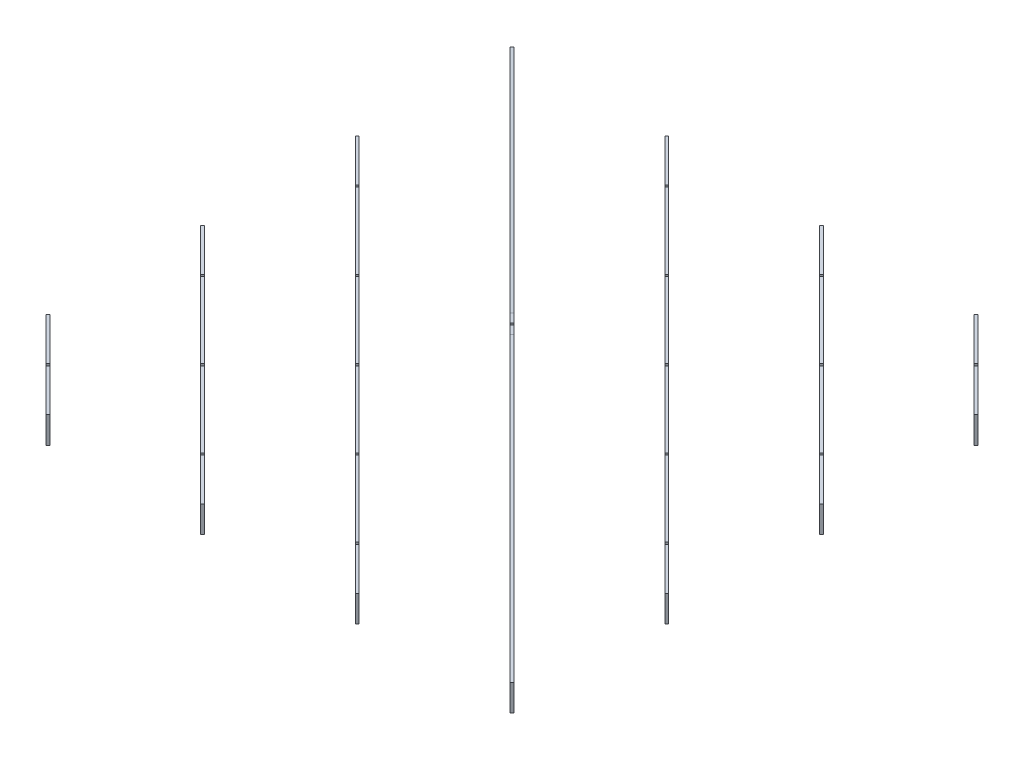
SolidWorks part; units mm, degrees
material "1.0553 (S355J0)"
ref_plane "Front" through (0, 0, 0) normal (0, 0, 1) x (1, 0, 0)
ref_plane "Top" through (0, 0, 0) normal (0, 1, 0) x (1, 0, 0)
ref_plane "Right" through (0, 0, 0) normal (1, 0, 0) x (0, 0, -1)
sketch "Sketch1" plane through (0, 0, 0) normal (0, 1, 0) x (1, 0, 0)
  line L0 (-525, -525) -> (-525, 525) construction
  line L1 (-625, 625) -> (625, 625) construction
  line L2 (-625, 625) -> (-625, -625) construction
  line L3 (-625, -625) -> (625, -625) construction
  line L4 (625, 625) -> (625, -625) construction
  line L5 (-625, 625) -> (625, -625) construction
  line L6 (-625, -625) -> (625, 625) construction
  line L7 (-525, 525) -> (525, 525) construction
  line L8 (-525, 350) -> (525, 350) construction
  line L9 (-525, 175) -> (525, 175) construction
  line L10 (-525, 0) -> (525, 0) construction
  line L11 (-525, -175) -> (525, -175) construction
  line L12 (-525, -350) -> (525, -350) construction
  line L13 (-525, -525) -> (525, -525) construction
  line L14 (-350, -525) -> (-350, 525) construction
  line L15 (-175, -525) -> (-175, 525) construction
  line L16 (0, -525) -> (0, 525) construction
  line L17 (175, -525) -> (175, 525) construction
  line L18 (350, -525) -> (350, 525) construction
  line L19 (525, -525) -> (525, 525) construction
  line L20 (-620, 625) -> (620, 625) construction
  line L23 (625, 620) -> (625, -620) construction
  point P0 (0, 0)
  dimension "D5" = 175
  dimension "D3" = 7
  dimension "D4" = 7
sketch "Sketch2" plane through (0, 0, 0) normal (0, 1, 0) x (1, 0, 0)
  line L0 (-625, 625) -> (625, -625) construction
  line L1 (622.8787, -622.8787) -> (-622.8787, -622.8787) construction
  line L2 (622.8787, -622.8787) -> (622.8787, 622.8787) construction
  line L3 (622.8787, 622.8787) -> (-622.8787, 622.8787) construction
  line L4 (-622.8787, -622.8787) -> (-622.8787, 622.8787) construction
  line L5 (622.8787, -622.8787) -> (-622.8787, 622.8787) construction
  line L6 (622.8787, 622.8787) -> (-622.8787, -622.8787) construction
  line L7 (-272.8787, 622.8787) -> (622.8787, -272.8787) construction
  line L8 (77.1213, 622.8787) -> (622.8787, 77.1213) construction
  line L9 (427.1213, 622.8787) -> (622.8787, 427.1213) construction
  line L10 (-622.8787, 272.8787) -> (272.8787, -622.8787) construction
  line L11 (-622.8787, -77.1213) -> (-77.1213, -622.8787) construction
  line L12 (-622.8787, -427.1213) -> (-427.1213, -622.8787) construction
  line L13 (-625, -429.2426) -> (-429.2426, -625)
  line L14 (-625, -79.2426) -> (-79.2426, -625)
  line L15 (-625, 270.7574) -> (270.7574, -625)
  line L16 (625, -620.7574) -> (-620.7574, 625)
  line L17 (-275, 620.7574) -> (620.7574, -275)
  line L18 (75, 620.7574) -> (620.7574, 75)
  line L19 (425, 620.7574) -> (620.7574, 425)
  line L20 (-620.7574, -425) -> (-425, -620.7574)
  line L21 (-620.7574, -75) -> (-75, -620.7574)
  line L22 (-620.7574, 275) -> (275, -620.7574)
  line L23 (620.7574, -625) -> (-625, 620.7574)
  line L24 (-270.7574, 625) -> (625, -270.7574)
  line L25 (79.2426, 625) -> (625, 79.2426)
  line L26 (429.2426, 625) -> (625, 429.2426)
  line L27 (-625, 625) -> (625, 625) construction
  line L29 (-625, -429.2426) -> (-620.7574, -425)
  line L30 (-429.2426, -625) -> (-425, -620.7574)
  line L31 (-625, -79.2426) -> (-620.7574, -75)
  line L32 (-79.2426, -625) -> (-75, -620.7574)
  line L33 (-625, 270.7574) -> (-620.7574, 275)
  line L34 (270.7574, -625) -> (275, -620.7574)
  line L35 (625, -620.7574) -> (620.7574, -625)
  line L36 (-620.7574, 625) -> (-625, 620.7574)
  line L37 (-275, 620.7574) -> (-270.7574, 625)
  line L38 (620.7574, -275) -> (625, -270.7574)
  line L39 (75, 620.7574) -> (79.2426, 625)
  line L40 (620.7574, 75) -> (625, 79.2426)
  line L41 (425, 620.7574) -> (429.2426, 625)
  line L42 (620.7574, 425) -> (625, 429.2426)
  point P0 (0, 0)
extrude "Boss-Extrude1" add sketch "Sketch2" along normal blind 60
sketch "Sketch4" plane through (-2.1213, 0, 2.1213) normal (-0.7071, 0, 0.7071) x (0.7071, 0, 0.7071)
  line L0 (0, 60) -> (0, 140) construction
  line L1 (-138.4214, 60) -> (138.4214, 60) construction
  line L2 (-30, 140) -> (-880.8835, 60)
  line L3 (-880.8835, 60) -> (-30, 60)
  line L4 (-30, 60) -> (-30, 140) construction
  line L5 (30, 140) -> (-30, 140)
  line L6 (880.8835, 60) -> (30, 60)
  line L7 (30, 140) -> (880.8835, 60)
  line L8 (-30, 60) -> (30, 60)
  dimension "D1" = 80
  dimension "D2" = 30
extrude "Boss-Extrude2" add sketch "Sketch4" against normal up to vertex
sketch "Sketch5" plane through (-527.1213, 0, 527.1213) normal (-0.7071, 0, 0.7071) x (0.7071, 0, 0.7071)
  line L0 (0, 0) -> (0, 60) construction
  line L1 (-138.4214, 60) -> (138.4214, 60) construction
  line L2 (-247.4874, 0) -> (-247.4874, 60) construction
  line L3 (494.9747, 0) -> (-247.4874, 0) construction
  line L4 (-742.4621, 0) -> (0, 0) construction
  line L5 (-385.9087, 60) -> (385.9087, 60) construction
  line L6 (-494.9747, 0) -> (-494.9747, 60) construction
  line L7 (247.4874, 0) -> (-494.9747, 0) construction
  line L8 (123.7437, 0) -> (-618.7184, 0) construction
  line L9 (-633.3961, 60) -> (633.3961, 60) construction
  line L10 (497.9747, 30) -> (491.9747, 90) construction
  line L11 (-250.4874, 90) -> (-244.4874, 90)
  line L12 (-250.4874, 90) -> (-250.4874, 30)
  line L13 (-250.4874, 30) -> (-244.4874, 30)
  line L14 (-244.4874, 90) -> (-244.4874, 30)
  line L15 (-250.4874, 90) -> (-244.4874, 30) construction
  line L16 (-250.4874, 30) -> (-244.4874, 90) construction
  line L17 (-497.9747, 90) -> (-491.9747, 90)
  line L18 (-497.9747, 90) -> (-497.9747, 30)
  line L19 (-497.9747, 30) -> (-491.9747, 30)
  line L20 (-491.9747, 90) -> (-491.9747, 30)
  line L21 (-497.9747, 90) -> (-491.9747, 30) construction
  line L22 (-497.9747, 30) -> (-491.9747, 90) construction
  line L23 (-3, 90) -> (3, 90)
  line L24 (-3, 90) -> (-3, 30)
  line L25 (-3, 30) -> (3, 30)
  line L26 (3, 90) -> (3, 30)
  line L27 (-3, 90) -> (3, 30) construction
  line L28 (-3, 30) -> (3, 90) construction
  line L29 (497.9747, 90) -> (491.9747, 30) construction
  line L30 (250.4874, 30) -> (244.4874, 90) construction
  line L31 (250.4874, 90) -> (244.4874, 30) construction
  line L32 (494.9747, 0) -> (494.9747, 60) construction
  line L33 (247.4874, 0) -> (247.4874, 60) construction
  line L34 (491.9747, 90) -> (491.9747, 30)
  line L35 (497.9747, 30) -> (491.9747, 30)
  line L36 (497.9747, 90) -> (497.9747, 30)
  line L37 (497.9747, 90) -> (491.9747, 90)
  line L38 (244.4874, 90) -> (244.4874, 30)
  line L39 (250.4874, 30) -> (244.4874, 30)
  line L40 (250.4874, 90) -> (250.4874, 30)
  line L41 (250.4874, 90) -> (244.4874, 90)
  circle A0 centre (-497.9747, 30) radius 1.5
  circle A1 centre (-491.9747, 30) radius 1.5
  circle A2 centre (-250.4874, 30) radius 1.5
  circle A3 centre (-244.4874, 30) radius 1.5
  circle A4 centre (-3, 30) radius 1.5
  circle A5 centre (3, 30) radius 1.5
  circle A6 centre (244.4874, 30) radius 1.5
  circle A7 centre (250.4874, 30) radius 1.5
  circle A8 centre (491.9747, 30) radius 1.5
  circle A9 centre (497.9747, 30) radius 1.5
  line M11 (138.4214, 60) -> (-138.4214, 60)
  dimension "D7" = 3
  dimension "D8" = 3
  dimension "D9" = 3
  dimension "D10" = 3
  dimension "D11" = 3
  dimension "D12" = 3
  dimension "D1" = 3
  dimension "D2" = 3
  dimension "D3" = 3
  dimension "D4" = 60
  dimension "D5" = 60
  dimension "D6" = 60
extrude "Cut-Extrude1" cut sketch "Sketch5" against normal up to surface (500.9747 mm away) contours L35 A9 L36 L37 L34 A8 | A8 L34 L35 | A8 L35 L34 | A9 L36 L35 | A9 L35 L36 | L39 A7 L40 L41 L38 A6 | A6 L38 L39 | A6 L39 L38 | A7 L39 L40 | A7 L40 L39 | A5 L26 L24 A4 L25 M11 | L25 A4 L24 | L24 A4 L25 | L26 A5 L25 | L25 A5 L26 | A3 L14 L11 L12 A2 L13 | L13 A2 L12 | L12 A2 L13 | L14 A3 L13 | L13 A3 L14 | A1 L20 L17 L18 A0 L19 | L19 A0 L18 | L18 A0 L19 | L20 A1 L19 | L19 A1 L20 up to face at (-172.8787, 30, 172.8787)
sketch "Sketch6" plane through (527.1213, 0, -527.1213) normal (0.7071, 0, -0.7071) x (-0.7071, 0, -0.7071)
  line L4 (-138.4214, 0) -> (138.4214, 0)
  line L5 (138.4214, 0) -> (138.4214, 60)
  line L6 (138.4214, 60) -> (-138.4214, 60)
  line L7 (-138.4214, 60) -> (-138.4214, 0)
  line L8 (-138.4214, 0) -> (138.4214, 0)
  line L9 (138.4214, 0) -> (138.4214, 60)
  line L10 (138.4214, 60) -> (-138.4214, 60)
  line L11 (-138.4214, 60) -> (-138.4214, 0)
  line L12 (497.9747, 90) -> (491.9747, 90)
  line L13 (491.9747, 90) -> (491.9747, 30)
  line L14 (491.9747, 30) -> (497.9747, 30)
  line L15 (497.9747, 30) -> (497.9747, 90)
  line L16 (497.9747, 90) -> (491.9747, 90)
  line L17 (491.9747, 90) -> (491.9747, 30)
  line L18 (491.9747, 30) -> (497.9747, 30)
  line L19 (497.9747, 30) -> (497.9747, 90)
  line L20 (250.4874, 90) -> (244.4874, 90)
  line L21 (244.4874, 90) -> (244.4874, 30)
  line L22 (244.4874, 30) -> (250.4874, 30)
  line L23 (250.4874, 30) -> (250.4874, 90)
  line L24 (250.4874, 90) -> (244.4874, 90)
  line L25 (244.4874, 90) -> (244.4874, 30)
  line L26 (244.4874, 30) -> (250.4874, 30)
  line L27 (250.4874, 30) -> (250.4874, 90)
  line L28 (-244.4874, 30) -> (-244.4874, 90)
  line L29 (-250.4874, 30) -> (-244.4874, 30)
  line L30 (-250.4874, 90) -> (-250.4874, 30)
  line L31 (-244.4874, 90) -> (-250.4874, 90)
  line L32 (-244.4874, 30) -> (-244.4874, 90)
  line L33 (-250.4874, 30) -> (-244.4874, 30)
  line L34 (-250.4874, 90) -> (-250.4874, 30)
  line L35 (-244.4874, 90) -> (-250.4874, 90)
  line L36 (-491.9747, 30) -> (-491.9747, 90)
  line L37 (-497.9747, 30) -> (-491.9747, 30)
  line L38 (-497.9747, 90) -> (-497.9747, 30)
  line L39 (-491.9747, 90) -> (-497.9747, 90)
  line L40 (-491.9747, 30) -> (-491.9747, 90)
  line L41 (-497.9747, 30) -> (-491.9747, 30)
  line L42 (-497.9747, 90) -> (-497.9747, 30)
  line L43 (-491.9747, 90) -> (-497.9747, 90)
  line L44 (3, 90) -> (-3, 90)
  line L45 (3, 30) -> (3, 90)
  line L46 (-3, 30) -> (3, 30)
  line L47 (-3, 90) -> (-3, 30)
  line L48 (3, 90) -> (-3, 90)
  line L49 (3, 30) -> (3, 90)
  line L50 (-3, 30) -> (3, 30)
  line L51 (-3, 90) -> (-3, 30)
  circle A1 centre (-3, 30) radius 1.5
  circle A2 centre (-3, 30) radius 1.5
  circle A3 centre (3, 30) radius 1.5
  circle A4 centre (3, 30) radius 1.5
  circle A5 centre (244.4874, 30) radius 1.5
  circle A6 centre (244.4874, 30) radius 1.5
  circle A7 centre (250.4874, 30) radius 1.5
  circle A8 centre (250.4874, 30) radius 1.5
  circle A9 centre (491.9747, 30) radius 1.5
  circle A10 centre (491.9747, 30) radius 1.5
  circle A11 centre (497.9747, 30) radius 1.5
  circle A12 centre (497.9747, 30) radius 1.5
  circle A13 centre (-497.9747, 30) radius 1.5
  circle A14 centre (-497.9747, 30) radius 1.5
  circle A15 centre (-491.9747, 30) radius 1.5
  circle A16 centre (-491.9747, 30) radius 1.5
  circle A17 centre (-250.4874, 30) radius 1.5
  circle A18 centre (-250.4874, 30) radius 1.5
  circle A19 centre (-244.4874, 30) radius 1.5
  circle A20 centre (-244.4874, 30) radius 1.5
  dimension "D1" = 0
  dimension "D2" = 0
  dimension "D3" = 0
  dimension "D4" = 0
  dimension "D5" = 0
  dimension "D6" = 0
  dimension "D7" = 0
  dimension "D8" = 0
  dimension "D9" = 0
  dimension "D10" = 0
  dimension "D11" = 0
  dimension "D12" = 0
  dimension "D13" = 0
  dimension "D14" = 0
  dimension "D15" = 0
  dimension "D16" = 0
extrude "Cut-Extrude2" cut sketch "Sketch6" against normal up to surface (500.9747 mm away) contours A16 L40 L43 L42 A14 L41 | L41 A14 L42 | L42 A14 L41 | L40 A16 L41 | L41 A16 L40 | A20 L32 L35 L34 A18 L33 | L33 A18 L34 | L34 A18 L33 | L32 A20 L33 | L33 A20 L32 | A4 L49 L10 L51 A2 L50 | L49 A4 L50 | L50 A4 L49 | L50 A2 L51 | L51 A2 L50 | L25 A6 L26 | L26 A6 L25 | A8 L27 L24 L25 A6 L26 | L27 A8 L26 | L26 A8 L27 | L17 A10 L18 | L18 A10 L17 | A12 L19 L16 L17 A10 L18 | L19 A12 L18 | L18 A12 L19 up to face at (172.8787, 30, -172.8787)
sketch "Sketch7" plane through (-2.1213, 0, 2.1213) normal (-0.7071, 0, 0.7071) x (0.7071, 0, 0.7071)
  line L0 (0, 140) -> (0, 0) construction
  line L1 (30, 140) -> (-30, 140) construction
  line L2 (123.7437, 0) -> (-618.7184, 0) construction
  line L3 (-3, 210) -> (3, 210)
  line L4 (-3, 210) -> (-3, 70)
  line L5 (-3, 70) -> (3, 70)
  line L6 (3, 210) -> (3, 70)
  line L7 (-3, 210) -> (3, 70) construction
  line L8 (-3, 70) -> (3, 210) construction
  line L9 (-250.4874, 30) -> (-244.4874, 30)
  line L10 (-250.4874, 30) -> (-250.4874, -30)
  line L11 (-250.4874, -30) -> (-244.4874, -30)
  line L12 (-244.4874, 30) -> (-244.4874, -30)
  line L13 (-250.4874, 30) -> (-244.4874, -30) construction
  line L14 (-250.4874, -30) -> (-244.4874, 30) construction
  line L15 (247.4874, 0) -> (-494.9747, 0) construction
  line L16 (-497.9747, 30) -> (-491.9747, 30)
  line L17 (-497.9747, 30) -> (-497.9747, -30)
  line L18 (-497.9747, -30) -> (-491.9747, -30)
  line L19 (-491.9747, 30) -> (-491.9747, -30)
  line L20 (-497.9747, 30) -> (-491.9747, -30) construction
  line L21 (-497.9747, -30) -> (-491.9747, 30) construction
  line L22 (-883.8835, 0) -> (883.8835, 0) construction
  line L23 (-742.4621, 0) -> (0, 0) construction
  line L24 (-745.4621, 30) -> (-739.4621, 30)
  line L25 (-745.4621, 30) -> (-745.4621, -30)
  line L26 (-745.4621, -30) -> (-739.4621, -30)
  line L27 (-739.4621, 30) -> (-739.4621, -30)
  line L28 (-745.4621, 30) -> (-739.4621, -30) construction
  line L29 (-745.4621, -30) -> (-739.4621, 30) construction
  line L30 (745.4621, -30) -> (739.4621, 30) construction
  line L31 (745.4621, 30) -> (739.4621, -30) construction
  line L32 (497.9747, -30) -> (491.9747, 30) construction
  line L33 (497.9747, 30) -> (491.9747, -30) construction
  line L34 (250.4874, -30) -> (244.4874, 30) construction
  line L35 (250.4874, 30) -> (244.4874, -30) construction
  line L36 (739.4621, 30) -> (739.4621, -30)
  line L37 (745.4621, -30) -> (739.4621, -30)
  line L38 (745.4621, 30) -> (745.4621, -30)
  line L39 (745.4621, 30) -> (739.4621, 30)
  line L40 (491.9747, 30) -> (491.9747, -30)
  line L41 (497.9747, -30) -> (491.9747, -30)
  line L42 (497.9747, 30) -> (497.9747, -30)
  line L43 (497.9747, 30) -> (491.9747, 30)
  line L44 (244.4874, 30) -> (244.4874, -30)
  line L45 (250.4874, -30) -> (244.4874, -30)
  line L46 (250.4874, 30) -> (250.4874, -30)
  line L47 (250.4874, 30) -> (244.4874, 30)
  circle A0 centre (-3, 70) radius 1.5
  circle A1 centre (3, 70) radius 1.5
  circle A2 centre (-250.4874, 30) radius 1.5
  circle A3 centre (-244.4874, 30) radius 1.5
  circle A4 centre (-491.9747, 30) radius 1.5
  circle A5 centre (-497.9747, 30) radius 1.5
  circle A6 centre (-739.4621, 30) radius 1.5
  circle A7 centre (-745.4621, 30) radius 1.5
  circle A8 centre (745.4621, 30) radius 1.5
  circle A9 centre (739.4621, 30) radius 1.5
  circle A10 centre (497.9747, 30) radius 1.5
  circle A11 centre (491.9747, 30) radius 1.5
  circle A12 centre (244.4874, 30) radius 1.5
  circle A13 centre (250.4874, 30) radius 1.5
  point P9 (-247.4874, 0)
  point P16 (-494.9747, 0)
  point P25 (-742.4621, 0)
  point P32 (0, 70)
  point P59 (742.4621, 0)
  point P60 (494.9747, 0)
  point P61 (247.4874, 0)
  line M15 (-880.8835, 0) -> (880.8835, 0)
  line M18 (30, 140) -> (-30, 140)
  dimension "D7" = 3
  dimension "D8" = 3
  dimension "D9" = 3
  dimension "D10" = 3
  dimension "D11" = 3
  dimension "D12" = 3
  dimension "D1" = 3
  dimension "D3" = 3
  dimension "D4" = 60
  dimension "D6" = 60
  dimension "D13" = 3
  dimension "D14" = 3
  dimension "D15" = 3
  dimension "D2" = 60
  dimension "D5" = 3
extrude "Cut-Extrude3" cut sketch "Sketch7" against normal up to next (6 mm away) contours L24 A7 L25 | L25 A7 L24 | A7 L25 L27 A6 L24 M15 | L24 A6 L27 | L27 A6 L24 | L16 A5 L17 | L17 A5 L16 | A5 L17 L19 A4 L16 M15 | L16 A4 L19 | L19 A4 L16 | L12 A3 L9 | L9 A3 L12 | A3 L9 A2 L10 L12 M15 | L10 A2 L9 | L9 A2 L10 | A1 L6 L4 A0 L5 M18 | L5 A0 L4 | L4 A0 L5 | L5 A1 L6 | L6 A1 L5 | A12 L44 L47 | A12 L47 L44 | L46 A13 L47 A12 L44 M15 | A13 L46 L47 | A13 L47 L46 | A11 L40 L43 | A11 L43 L40 | L43 A11 L40 L42 A10 M15 | A10 L42 L43 | A10 L43 L42 | A9 L36 L39 | A9 L39 L36 | L39 A9 L36 L38 A8 M15 | A8 L38 L39 | A8 L39 L38
equation "\"D1@Boss-Extrude1\"=\"Plate width\""
equation "\"Plate width\"= 60"
equation "\"D1@Sketch5\"=\"Half rib thickness\""
equation "\"D2@Sketch5\"=\"Half rib thickness\""
equation "\"D3@Sketch5\"=\"Half rib thickness\""
equation "\"D4@Sketch5\"=\"Plate width\""
equation "\"D5@Sketch5\"=\"Plate width\""
equation "\"D6@Sketch5\"=\"Plate width\""
equation "\"D7@Sketch5\"=\"Half rib thickness\""
equation "\"D8@Sketch5\"=\"Half rib thickness\""
equation "\"D9@Sketch5\"=\"Half rib thickness\""
equation "\"D10@Sketch5\"=\"Half rib thickness\""
equation "\"D11@Sketch5\"=\"Half rib thickness\""
equation "\"D12@Sketch5\"=\"Half rib thickness\""
equation "\"D1@Sketch7\"=\"Half rib thickness\""
equation "\"D2@Sketch7\"=\"Plate width\""
equation "\"D3@Sketch7\"=\"Half rib thickness\""
equation "\"D4@Sketch7\"=\"Plate width\""
equation "\"D5@Sketch7\"=\"Half rib thickness\""
equation "\"D6@Sketch7\"=\"Plate width\""
equation "\"D7@Sketch7\"=\"Half rib thickness\""
equation "\"D8@Sketch7\"=\"Half rib thickness\""
equation "\"D9@Sketch7\"=\"Half rib thickness\""
equation "\"D10@Sketch7\"=\"Half rib thickness\""
equation "\"D11@Sketch7\"=\"Half rib thickness\""
equation "\"D12@Sketch7\"=\"Half rib thickness\""
equation "\"D13@Sketch7\"=\"Half rib thickness\""
equation "\"D14@Sketch7\"=\"Half rib thickness\""
equation "\"D15@Sketch7\"=\"Half rib thickness\""
